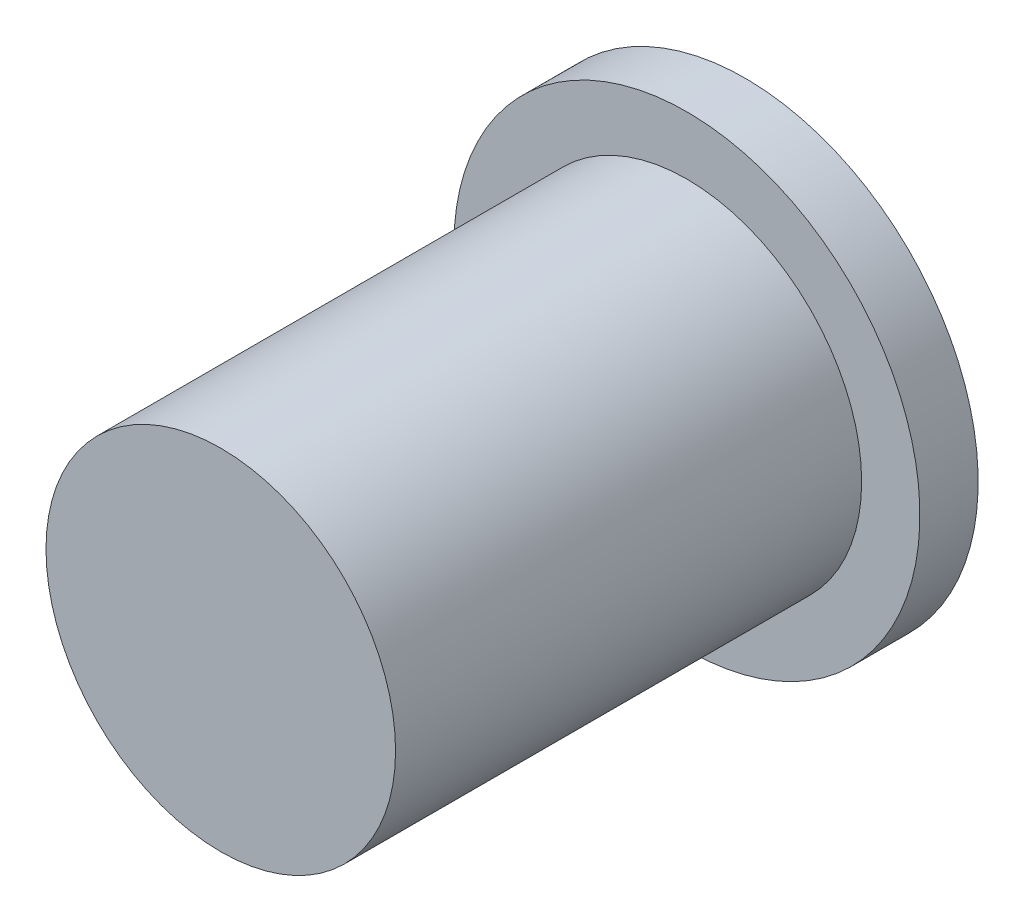
SolidWorks part; units mm, degrees
ref_plane "Front" through (0, 0, 0) normal (0, 0, 1) x (1, 0, 0)
ref_plane "Top" through (0, 0, 0) normal (0, 1, 0) x (1, 0, 0)
ref_plane "Right" through (0, 0, 0) normal (1, 0, 0) x (0, 0, -1)
sketch "Sketch1" plane through (0, 0, 0) normal (0, 0, 1) x (1, 0, 0)
  circle A0 centre (0, 0) radius 15
extrude "Boss-Extrude1" add sketch "Sketch1" along normal blind 40
sketch "Sketch2" plane through (0, 0, 0) normal (0, 0, -1) x (-1, 0, 0)
  circle A0 centre (0, 0) radius 20
extrude "Boss-Extrude2" add sketch "Sketch2" along normal blind 5
